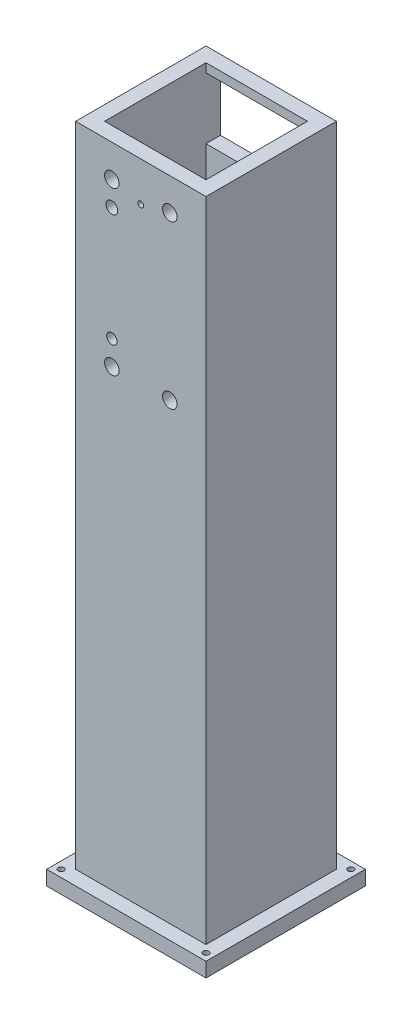
SolidWorks part; units mm, degrees
material "ABS"
ref_plane "Alzado" through (0, 0, 0) normal (0, 0, 1) x (1, 0, 0)
ref_plane "Planta" through (0, 0, 0) normal (0, 1, 0) x (1, 0, 0)
ref_plane "Vista lateral" through (0, 0, 0) normal (1, 0, 0) x (0, 0, -1)
sketch "Croquis1" plane through (0, 0, 0) normal (0, 1, 0) x (1, 0, 0)
  line L1 (-22.5, -22.5) -> (22.5, -22.5)
  line L2 (-22.5, -22.5) -> (-22.5, 22.5)
  line L3 (-22.5, 22.5) -> (22.5, 22.5)
  line L4 (22.5, -22.5) -> (22.5, 22.5)
  line L5 (-22.5, -22.5) -> (22.5, 22.5) construction
  line L6 (-22.5, 22.5) -> (22.5, -22.5) construction
  point P0 (0, 0)
  dimension "D1" = 45
  dimension "D2" = 45
extrude "Saliente-Extruir1" add sketch "Croquis1" along normal blind 300
sketch "Croquis4" plane through (-22.5, 0, 0) normal (-1, 0, 0) x (0, 0, 1)
  line L1 (22.5, 300) -> (22.5, 0) construction
  line L3 (55, 0) -> (-55, 0) construction
  line L5 (4.5, 0) -> (4.5, 34)
  line L6 (4.5, 34) -> (22.5, 34)
  line L8 (22.5, 34) -> (22.5, 0)
  line L9 (22.5, 0) -> (4.5, 0)
  dimension "D4" = 34
extrude "Cortar-Extruir2" cut sketch "Croquis4" against normal through all
sketch "Croquis7" plane through (0, 0, 22.5) normal (0, 0, 1) x (1, 0, 0)
  line L0 (0, -24.75) -> (0, 24.75) construction
  line L1 (-22.5, 246.3879) -> (22.5, 246.3879)
  line L2 (-22.5, 246.3879) -> (-22.5, 273.6121)
  line L3 (-22.5, 273.6121) -> (22.5, 273.6121)
  line L4 (22.5, 246.3879) -> (22.5, 273.6121)
  line L5 (-22.5, 246.3879) -> (22.5, 273.6121) construction
  line L6 (-22.5, 273.6121) -> (22.5, 246.3879) construction
  line L7 (22.5, 300) -> (22.5, 34) construction
  point P0 (0, 260)
  dimension "D1" = 260
sketch "Croquis8" plane through (0, 300, 0) normal (0, 1, 0) x (1, 0, 0)
  line L0 (22.5, -22.5) -> (22.5, 22.5) construction
  line L1 (-17.5, -17.5) -> (17.5, -17.5)
  line L2 (-17.5, -17.5) -> (-17.5, 17.5)
  line L3 (-17.5, 17.5) -> (17.5, 17.5)
  line L4 (17.5, -17.5) -> (17.5, 17.5)
  line L5 (-17.5, -17.5) -> (17.5, 17.5) construction
  line L6 (-17.5, 17.5) -> (17.5, -17.5) construction
  line L7 (22.5, 22.5) -> (-22.5, 22.5) construction
  point P0 (0, 0)
  dimension "D1" = 5
  dimension "D2" = 5
extrude "Cortar-Extruir3" cut sketch "Croquis8" against normal through all contours L3 L4 L1 L2
sketch "Croquis9" plane through (0, 0, -22.5) normal (0, 0, -1) x (-1, 0, 0)
  line L0 (22.5, 273.6121) -> (-22.5, 246.3879) construction
  line L1 (-17.5, 249.4128) -> (17.5, 249.4128)
  line L2 (-17.5, 249.4128) -> (-17.5, 270.5872)
  line L3 (-17.5, 270.5872) -> (17.5, 270.5872)
  line L4 (17.5, 249.4128) -> (17.5, 270.5872)
  line L5 (-17.5, 249.4128) -> (17.5, 270.5872) construction
  line L6 (-17.5, 270.5872) -> (17.5, 249.4128) construction
  line L7 (22.5, 246.3879) -> (22.5, 273.6121) construction
  point P0 (0, 260)
  point P10 (22.5, 260)
  dimension "D1" = 5
extrude "Cortar-Extruir4" cut sketch "Croquis9" against normal blind 10 contours L4 L3 L2 L1
sketch "Croquis10" plane through (0, 0, 22.5) normal (0, 0, 1) x (1, 0, 0)
  circle A0 centre (0, 260) radius 1
  dimension "D1" = 2
extrude "Cortar-Extruir5" cut sketch "Croquis10" against normal blind 10
sketch "Croquis11" plane through (0, 0, 22.5) normal (0, 0, 1) x (1, 0, 0)
  line L0 (22.5, 300) -> (22.5, 34) construction
  line L1 (-22.5, 300) -> (22.5, 300)
  line L2 (-22.5, 300) -> (-22.5, 273.6121)
  line L3 (-22.5, 273.6121) -> (22.5, 273.6121)
  line L4 (22.5, 300) -> (22.5, 273.6121)
  line L5 (-22.5, 273.6121) -> (22.5, 273.6121) construction
  dimension "D1" = 0
extrude "Cortar-Extruir6" cut sketch "Croquis11" against normal through all
sketch "Croquis12" plane through (0, 0, 22.5) normal (0, 0, 1) x (1, 0, 0)
  line L0 (-22.5, 267.3717) -> (22.5, 246.3879)
  line L1 (-22.5, 246.3879) -> (-22.5, 273.6121) construction
  line L2 (-22.5, 246.3879) -> (22.5, 246.3879) construction
  dimension "D1" = 25
sketch "Croquis13" plane through (0, 0, 0) normal (1, 0, 0) x (0, 0, -1)
  line L0 (-22.5, 273.6121) -> (-22.5, 34) construction
  line L1 (-22.5, 50) -> (22.5, 50)
  line L2 (-22.5, 50) -> (-22.5, 0)
  line L3 (-22.5, 0) -> (22.5, 0)
  line L4 (22.5, 50) -> (22.5, 0)
  line L5 (24.75, 0) -> (-24.75, 0) construction
  line L6 (22.5, 273.6121) -> (22.5, 0) construction
  dimension "D1" = 50
extrude "Cortar-Extruir7" cut sketch "Croquis13" against normal through all both and the other way through all
sketch "Croquis14" plane through (0, 50, 0) normal (0, -1, 0) x (1, 0, 0)
  line L1 (-27.5, -27.5) -> (27.5, -27.5)
  line L2 (-27.5, -27.5) -> (-27.5, 27.5)
  line L3 (-27.5, 27.5) -> (27.5, 27.5)
  line L4 (27.5, -27.5) -> (27.5, 27.5)
  line L5 (-27.5, -27.5) -> (27.5, 27.5) construction
  line L6 (-27.5, 27.5) -> (27.5, -27.5) construction
  point P0 (0, 0)
  dimension "D1" = 27.5
  dimension "D2" = 27.5
extrude "Saliente-Extruir2" add sketch "Croquis14" along normal blind 5 contours L3 L4 L1 L2
sketch "Croquis16" plane through (0, 45, 0) normal (0, -1, 0) x (1, 0, 0)
  circle A0 centre (25, 25) radius 1
  circle A1 centre (-25, 25) radius 1
  circle A2 centre (-25, -25) radius 1
  circle A3 centre (25, -25) radius 1
  dimension "D1" = 2
  dimension "D2" = 2.5
  dimension "D3" = 2.5
  dimension "D4" = 2.5
  dimension "D5" = 2.5
extrude "Cortar-Extruir8" cut sketch "Croquis16" against normal through all both
sketch "Croquis17" plane through (0, 0, 22.5) normal (0, 0, 1) x (1, 0, 0)
  line L0 (0, -24.75) -> (0, 24.75) construction
  circle A0 centre (-10, 262.5026) radius 2.5
  circle A1 centre (-10, 254.1026) radius 2.03
  circle A2 centre (-10, 214.9026) radius 1.7933
  circle A3 centre (-10, 206.5026) radius 2.5
  circle A4 centre (10, 262.5026) radius 2.5
  circle A5 centre (10, 206.5026) radius 2.5
  dimension "D1" = 5
  dimension "D2" = 4.06
  dimension "D3" = 20
  dimension "D4" = 10
  dimension "D5" = 8.4
  dimension "D6" = 8.4
  dimension "D7" = 56
extrude "Cortar-Extruir9" cut sketch "Croquis17" against normal through all both and the other way through all
